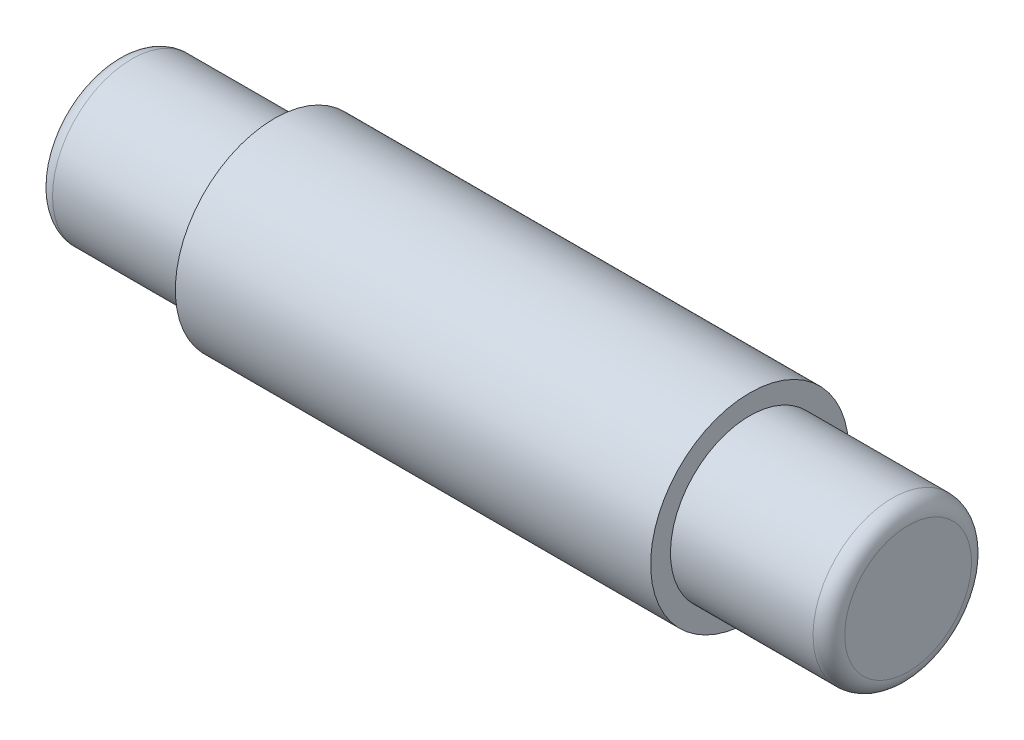
SolidWorks part; units mm, degrees
ref_plane "Front Plane" through (0, 0, 0) normal (0, 0, 1) x (1, 0, 0)
ref_plane "Top Plane" through (0, 0, 0) normal (0, 1, 0) x (1, 0, 0)
ref_plane "Right Plane" through (0, 0, 0) normal (1, 0, 0) x (0, 0, -1)
sketch "Sketch1" plane through (0, 0, 0) normal (0, 0, 1) x (1, 0, 0)
  line L0 (-63.5, 0) -> (63.5, 0)
  line L1 (63.5, 0) -> (63.5, 12.7)
  line L2 (63.5, 12.7) -> (38.1, 12.7)
  line L3 (38.1, 12.7) -> (38.1, 15.875)
  line L4 (38.1, 15.875) -> (-38.1, 15.875)
  line L5 (-38.1, 15.875) -> (-38.1, 12.7)
  line L6 (-38.1, 12.7) -> (-63.5, 12.7)
  line L7 (-63.5, 12.7) -> (-63.5, 0)
  dimension "D1" = 127
  dimension "D2" = 76.2
  dimension "D3" = 12.7
  dimension "D5" = 15.875
revolve "Revolve2" add sketch "Sketch1" angle 360 about L0
fillet "Fillet1" radius 2.54 2 edges at (-63.5, -12.7, 0) (63.5, -12.7, 0)
